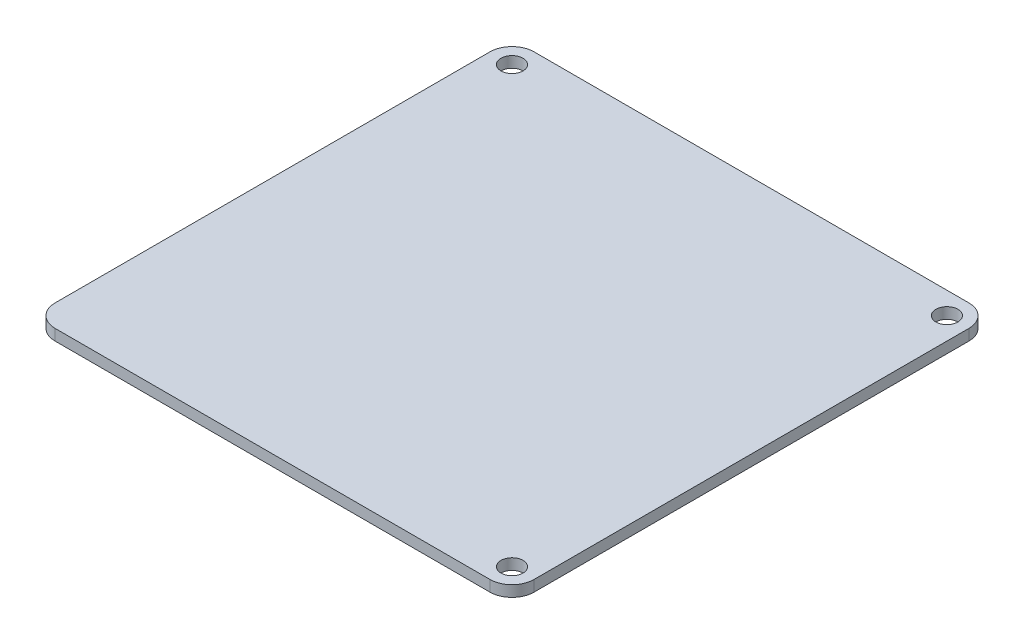
SolidWorks part; units mm, degrees
ref_plane "Front Plane" through (0, 0, 0) normal (0, 0, 1) x (1, 0, 0)
ref_plane "Top Plane" through (0, 0, 0) normal (0, 1, 0) x (1, 0, 0)
ref_plane "Right Plane" through (0, 0, 0) normal (1, 0, 0) x (0, 0, -1)
sketch "Sketch1" plane through (0, 0, 0) normal (0, 1, 0) x (1, 0, 0)
  line B0 (130.6177, -2.0846) -> (130.6177, 123.1766)
  line B1 (124.2677, 129.5266) -> (-0.9935, 129.5266)
  line B2 (-7.3435, 123.1766) -> (-7.3435, -2.0846)
  line B3 (-0.9935, -8.4346) -> (124.2677, -8.4346)
  line B4 (0, 44.6714) -> (0, 0)
  line B5 (5.3565, 116.8266) -> (5.3565, 50.9432)
  line B6 (117.9177, 116.8266) -> (5.3565, 116.8266)
  line B7 (117.9177, 4.2654) -> (117.9177, 116.8266)
  line B8 (20.2475, 4.2654) -> (117.9177, 4.2654)
  line B9 (0, 0) -> (14.2494, 0)
  circle B10 centre (-0.9935, 123.1766) radius 3.175
  arc B11 (130.6177, 123.1766) -> (124.2677, 129.5266) centre (124.2677, 123.1766) ccw
  arc B12 (-0.9935, 129.5266) -> (-7.3435, 123.1766) centre (-0.9935, 123.1766) ccw
  arc B13 (-7.3435, -2.0846) -> (-0.9935, -8.4346) centre (-0.9935, -2.0846) ccw
  arc B14 (124.2677, -8.4346) -> (130.6177, -2.0846) centre (124.2677, -2.0846) ccw
  circle B15 centre (124.2677, 123.1766) radius 3.175
  circle B16 centre (124.2677, -2.0846) radius 3.175
  arc B17 (0, 44.6714) -> (5.3565, 50.9432) centre (-0.9935, 50.9432) ccw
  arc B18 (20.2475, 4.2654) -> (14.2494, 0) centre (20.2475, -2.0846) ccw
sketch_block_instance "Block-Electronics Top-1"
sketch_block "Block-Electronics Top"
extrude "Boss-Extrude1" add sketch "Sketch1" along normal blind 3.175 contours B18 B8 B7 B6 B5 B17 B4 B9 | B3 B14 B0 B11 B1 B12 B2 B13 B16 B15 B10 B8 B18 B9 B4 B17 B5 B6 B7
